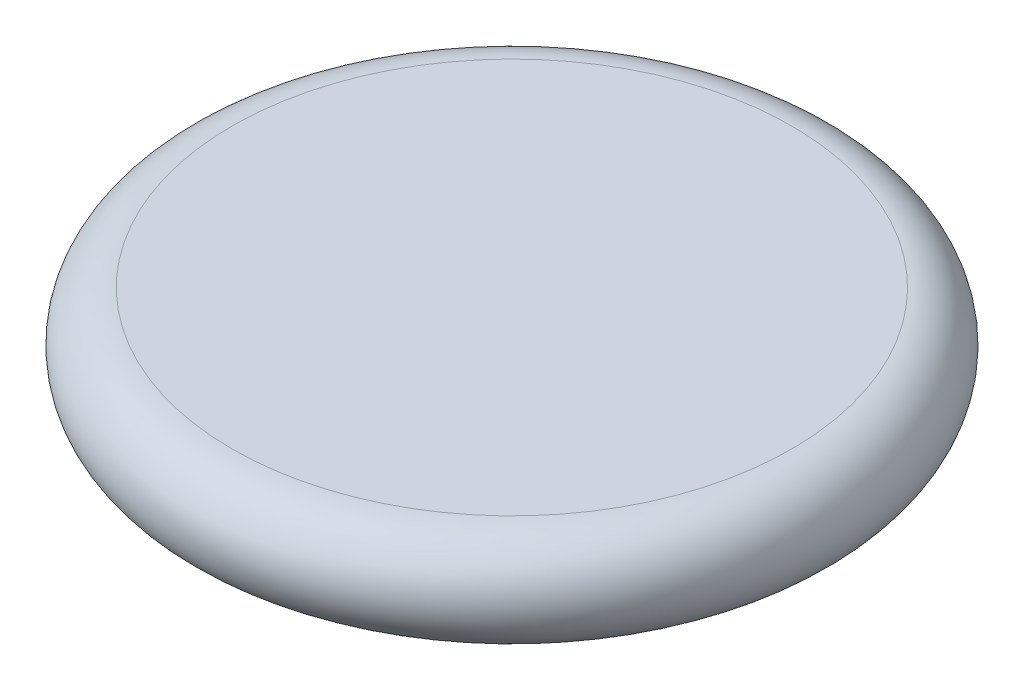
SolidWorks part; units mm, degrees
ref_plane "Спереди" through (0, 0, 0) normal (0, 0, 1) x (1, 0, 0)
ref_plane "Сверху" through (0, 0, 0) normal (0, 1, 0) x (1, 0, 0)
ref_plane "Справа" through (0, 0, 0) normal (1, 0, 0) x (0, 0, -1)
sketch "Эскиз1" plane through (0, 0, 0) normal (0, 0, 1) x (1, 0, 0)
  line L0 (0, 37.7) -> (0, -33.7348) construction
  line L1 (65.8199, 11.7236) -> (0, 11.7236)
  line L2 (65.8199, -11.7236) -> (0, -11.7236)
  line L3 (0, 11.7236) -> (0, -11.7236)
  arc A0 (65.8199, -11.7236) -> (65.8199, 11.7236) centre (65.8199, 0) ccw
revolve "Повернуть1" add sketch "Эскиз1" angle 360 about L0
